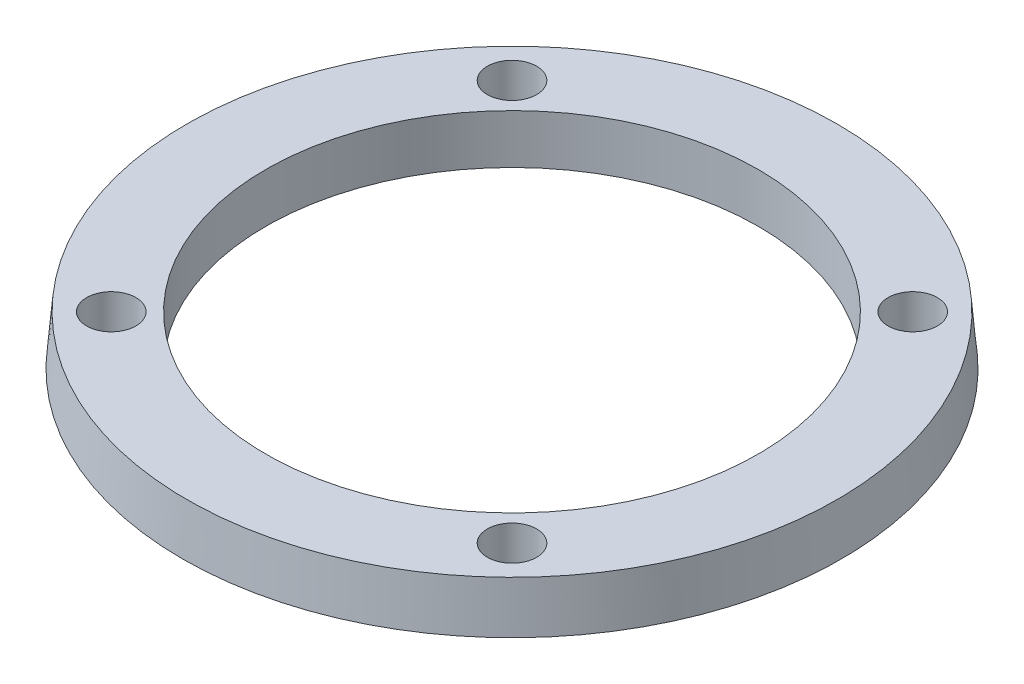
SolidWorks part; units mm, degrees
ref_plane "Спереди" through (0, 0, 0) normal (0, 0, 1) x (1, 0, 0)
ref_plane "Сверху" through (0, 0, 0) normal (0, 1, 0) x (1, 0, 0)
ref_plane "Справа" through (0, 0, 0) normal (1, 0, 0) x (0, 0, -1)
sketch "Sketch1" plane through (0, 0, 0) normal (0, 0, 1) x (1, 0, 0)
  line L0 (0, 0) -> (0, 18.1485) construction
  line L1 (-26.75, 0) -> (-26.4, 4)
  line L2 (-20, 0) -> (-26.75, 0)
  line L3 (-20, 0) -> (-20, 4)
  line L4 (-20, 4) -> (-26.4, 4)
  dimension "D1" = 40
  dimension "D2" = 53.5
  dimension "D3" = 4
  dimension "D4" = 5
revolve "Revolve1" add sketch "Sketch1" angle 360 about L0
sketch "Sketch3" plane through (0, 0, 0) normal (0, -1, 0) x (1, 0, 0)
  line L0 (0, 28.4408) -> (0, -30.4288) construction
  line L1 (-30.2044, 0) -> (32.513, 0) construction
  line L2 (-22.0442, 22.0442) -> (23.9683, -23.9683) construction
  line L3 (23.8428, 23.8428) -> (-25.0336, -25.0336) construction
  circle A0 centre (-16.2635, 16.2635) radius 2
  circle A1 centre (16.2635, 16.2635) radius 2
  circle A2 centre (-16.2635, -16.2635) radius 2
  circle A3 centre (16.2635, -16.2635) radius 2
  dimension "D2" = 4
  dimension "D1" = 45
  dimension "D3" = 46
extrude "Cut-Extrude1" cut sketch "Sketch3" against normal through all
